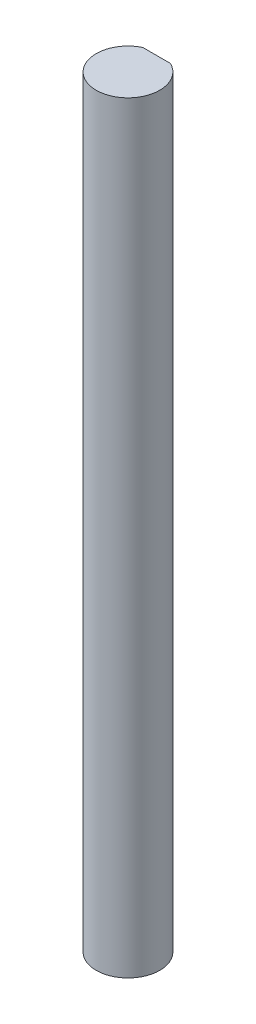
SolidWorks part; units mm, degrees
ref_plane "Front Plane" through (0, 0, 0) normal (0, 0, 1) x (1, 0, 0)
ref_plane "Top Plane" through (0, 0, 0) normal (0, 1, 0) x (1, 0, 0)
ref_plane "Right Plane" through (0, 0, 0) normal (1, 0, 0) x (0, 0, -1)
sketch "Sketch1" plane through (0, 0, 0) normal (0, 1, 0) x (1, 0, 0)
  line L1 (-1.0897, 2.25) -> (1.0897, 2.25)
  arc A0 (-1.0897, 2.25) -> (1.0897, 2.25) centre (0, 0) ccw
  dimension "D1" = 2.5
  dimension "D2" = 2.25
extrude "Boss-Extrude1" add sketch "Sketch1" along normal blind 60
